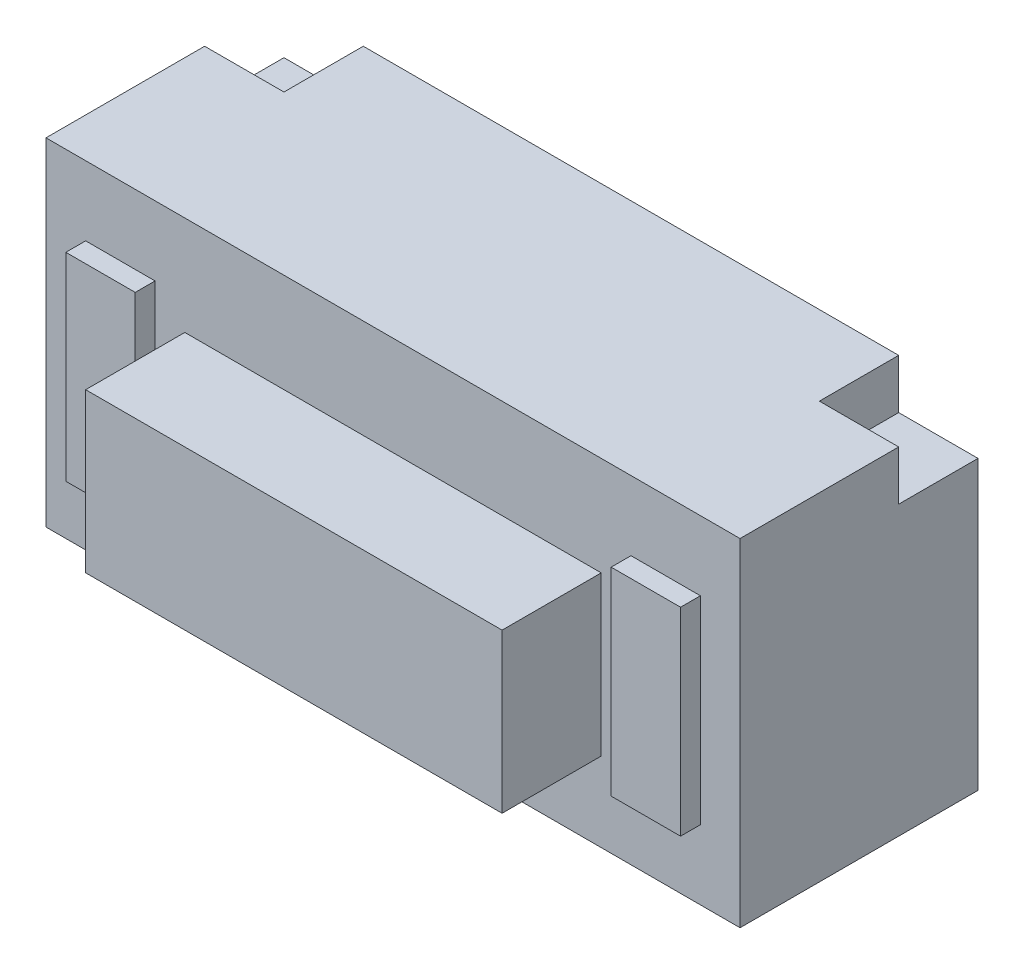
SolidWorks part; units mm, degrees
ref_plane "Plan de face" through (0, 0, 0) normal (0, 0, 1) x (1, 0, 0)
ref_plane "Plan de dessus" through (0, 0, 0) normal (0, 1, 0) x (1, 0, 0)
ref_plane "Plan de droite" through (0, 0, 0) normal (1, 0, 0) x (0, 0, -1)
sketch "Esquisse1" plane through (0, 0, 0) normal (0, 1, 0) x (1, 0, 0)
  line L1 (-3.5, -1.2) -> (3.5, -1.2)
  line L2 (-3.5, -1.2) -> (-3.5, 1.2)
  line L3 (-3.5, 1.2) -> (3.5, 1.2)
  line L4 (3.5, -1.2) -> (3.5, 1.2)
  line L5 (-3.5, -1.2) -> (3.5, 1.2) construction
  line L6 (-3.5, 1.2) -> (3.5, -1.2) construction
  point P0 (0, 0)
  dimension "D1" = 7
  dimension "D2" = 2.4
extrude "Boss.-Extru.1" add sketch "Esquisse1" along normal blind 3.4
sketch "Esquisse2" plane through (0, 3.4, 0) normal (0, 1, 0) x (1, 0, 0)
  line L1 (-3.5, 1.2) -> (-2.7, 1.2)
  line L2 (-3.5, 1.2) -> (-3.5, 0.4)
  line L3 (-3.5, 0.4) -> (-2.7, 0.4)
  line L4 (-2.7, 1.2) -> (-2.7, 0.4)
  line L5 (3.5, 1.2) -> (2.7, 1.2)
  line L6 (3.5, 1.2) -> (3.5, 0.4)
  line L7 (3.5, 0.4) -> (2.7, 0.4)
  line L8 (2.7, 1.2) -> (2.7, 0.4)
  dimension "D1" = 0.8
extrude "Enlèv. mat.-Extru.1" cut sketch "Esquisse2" against normal blind 0.5
sketch "Esquisse3" plane through (0, 0, 1.2) normal (0, 0, 1) x (1, 0, 0)
  line L0 (-3.5, 3.4) -> (-3.5, 0) construction
  line L1 (-3.1, 2.7) -> (-2.4, 2.7)
  line L2 (-3.1, 2.7) -> (-3.1, 0.7)
  line L3 (-3.1, 0.7) -> (-2.4, 0.7)
  line L4 (-2.4, 2.7) -> (-2.4, 0.7)
  line L5 (-2.1, 2.4) -> (2.1, 2.4)
  line L6 (-2.1, 2.4) -> (-2.1, 0.8)
  line L7 (-2.1, 0.8) -> (2.1, 0.8)
  line L8 (2.1, 2.4) -> (2.1, 0.8)
  line L9 (2.4, 2.7) -> (3.1, 2.7)
  line L10 (2.4, 2.7) -> (2.4, 0.7)
  line L11 (2.4, 0.7) -> (3.1, 0.7)
  line L12 (3.1, 2.7) -> (3.1, 0.7)
  line L13 (3.5, 3.4) -> (3.5, 0) construction
  line L14 (-3.5, 0) -> (3.5, 0) construction
  line L15 (-3.5, 3.4) -> (3.5, 3.4) construction
  dimension "D1" = 0.7
  dimension "D2" = 0.4
  dimension "D3" = 0.4
  dimension "D4" = 0.7
  dimension "D5" = 0.8
  dimension "D6" = 1
  dimension "D7" = 0.3
  dimension "D8" = 0.3
  dimension "D9" = 0.7
extrude "Boss.-Extru.2" add sketch "Esquisse3" along normal blind 0.2
sketch "Esquisse4" plane through (0, 0, 1.4) normal (0, 0, 1) x (1, 0, 0)
  line L4 (-2.1, 2.4) -> (-2.1, 0.8)
  line L5 (-2.1, 0.8) -> (2.1, 0.8)
  line L6 (2.1, 0.8) -> (2.1, 2.4)
  line L7 (2.1, 2.4) -> (-2.1, 2.4)
  line L8 (-2.1, 2.4) -> (-2.1, 0.8)
  line L9 (-2.1, 0.8) -> (2.1, 0.8)
  line L10 (2.1, 0.8) -> (2.1, 2.4)
  line L11 (2.1, 2.4) -> (-2.1, 2.4)
  dimension "D1" = 0
extrude "Boss.-Extru.3" add sketch "Esquisse4" along normal blind 0.8
sketch "Esquisse5" [suppressed] plane through (0, 0, 0) normal (0, -1, 0) x (1, 0, 0)
  line L0 (3.5, -1.2) -> (-3.5, -1.2) construction
  line L1 (-3.5, 1.2) -> (-4.1, 1.2)
  line L2 (-3.5, 1.2) -> (-3.5, 0.6)
  line L3 (-3.5, 0.6) -> (-4.1, 0.6)
  line L4 (-4.1, 1.2) -> (-4.1, 0.6)
  line L5 (-2.9, -1.2) -> (-2.3, -1.2)
  line L6 (-2.9, -1.2) -> (-2.9, -1.8)
  line L7 (-2.9, -1.8) -> (-2.3, -1.8)
  line L8 (-2.3, -1.2) -> (-2.3, -1.8)
  line L9 (-3.5, -1.2) -> (-2.9, -1.2) construction
  line L10 (2.9, -1.2) -> (2.3, -1.2)
  line L11 (2.9, -1.2) -> (2.9, -1.8)
  line L12 (2.9, -1.8) -> (2.3, -1.8)
  line L13 (2.3, -1.2) -> (2.3, -1.8)
  line L14 (3.5, 1.2) -> (4.1, 1.2)
  line L15 (3.5, 1.2) -> (3.5, 0.6)
  line L16 (3.5, 0.6) -> (4.1, 0.6)
  line L17 (4.1, 1.2) -> (4.1, 0.6)
  line L18 (2.9, -1.2) -> (3.5, -1.2) construction
  dimension "D1" = 0.6
extrude "Boss.-Extru.4" [suppressed] add sketch "Esquisse5" against normal blind 0.1 separate body
